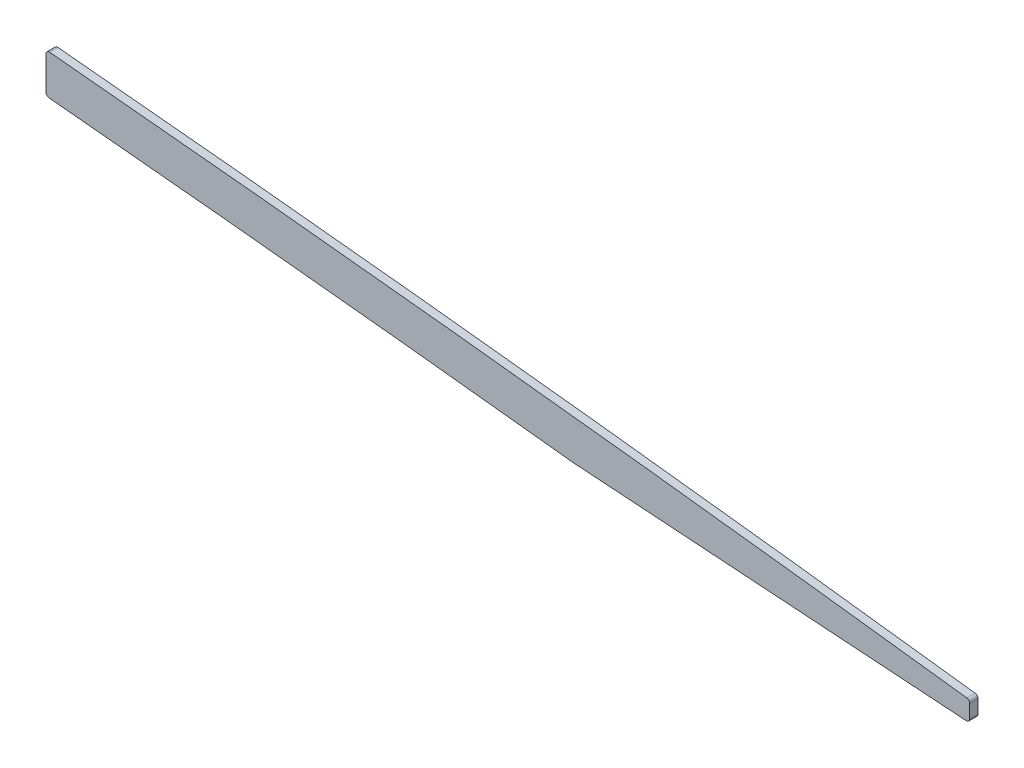
SolidWorks part; units mm, degrees
material "Plywood"
ref_plane "Front Plane" through (0, 0, 0) normal (0, 0, 1) x (1, 0, 0)
ref_plane "Top Plane" through (0, 0, 0) normal (0, 1, 0) x (1, 0, 0)
ref_plane "Right Plane" through (0, 0, 0) normal (1, 0, 0) x (0, 0, -1)
sketch "Sketch2" plane through (0, 0, 0) normal (0, 0, 1) x (1, 0, 0)
  line L0 (0, 0) -> (266.9553, 0) construction
  line L1 (825.5, 263.7287) -> (825.5, 174.6622)
  line L2 (2311.4, 135.8299) -> (2311.4, 52.664)
  line L3 (2665.4125, 96.9963) -> (2665.4125, 81.6353)
  line L4 (2665.4125, 89.3583) -> (2513.3711, 99.8062)
  spline S0 degree 5 poles (818.067, 264.7065) (827.0431, 263.4992) (836.0291, 262.3734) (845.0868, 261.3058) (891.3865, 256.087) (937.6862, 251.7792) (973.4521, 248.2277) (1071.9467, 239.0511) (1170.4413, 229.7315) (1231.7919, 224.5039) (1324.8993, 216.7906) (1418.0067, 209.0401) (1449.7429, 206.3618) (1636.9286, 190.5211) (1824.1143, 175.4092) (1979.9669, 164.2997) (2156.2686, 150.4144) (2332.5703, 133.8572) (2354.213, 131.7851) (2436.3555, 123.724) (2518.4981, 114.8591) (2579.4813, 107.7425) (2639.6368, 100.3834) (2699.7923, 92.6045) knots 77.930822 77.930822 77.930822 77.930822 77.930822 77.930822 82.465793 82.465793 82.465793 100.79329 100.79329 100.79329 131.098954 131.098954 131.098954 146.769198 146.769198 146.769198 223.533959 223.533959 223.533959 233.943117 233.943117 233.943117 264.216209 264.216209 264.216209 264.216209 264.216209 264.216209 weights 1 1 1 1 1 1 1 1 1 1 1 1 1 1 1 1 1 1 1 1 1 1 1 1
  spline S1 degree 1 poles (816.0355, 249.6025) (2697.8379, 77.4903) knots 0 0 1 1 construction
  spline S2 degree 3 poles (816.0355, 249.6025) (820.896, 248.9488) (830.6112, 247.6997) (845.2811, 245.9534) (860.0865, 244.2956) (879.8307, 242.1866) (904.37, 239.6983) (933.571, 236.8322) (962.6427, 234.0237) (991.7626, 231.242) (1021.072, 228.4759) (1060.3764, 224.797) (1109.513, 220.1844) (1168.5112, 214.8171) (1227.5001, 209.6621) (1306.1332, 203.0212) (1404.3615, 194.9207) (1522.2399, 184.9181) (1640.1829, 175.167) (1758.1654, 165.7576) (1876.1554, 156.5909) (1994.0875, 147.4533) (2092.2687, 139.6242) (2170.748, 133.0797) (2219.7717, 128.8422) (2258.984, 125.3472) (2288.3795, 122.6709) (2317.8122, 119.9317) (2347.5515, 117.1004) (2377.1599, 114.2101) (2406.4697, 111.269) (2435.8183, 108.2401) (2469.0247, 104.7153) (2497.3133, 101.6123) (2518.2453, 99.2591) (2543.5949, 96.3824) (2583.4681, 91.7389) (2626.5047, 86.5072) (2656.9573, 82.7047) (2676.2281, 80.2695) (2689.7296, 78.5389) (2697.8379, 77.4903) knots 77.930822 77.930822 77.930822 77.930822 79.386176 80.841531 82.296885 83.75224 86.662949 89.573658 92.484367 95.395077 98.305786 101.216495 107.037913 112.859332 118.68075 124.502168 136.145005 147.787842 159.430678 171.073515 182.716352 194.359189 206.002025 211.823444 217.644862 220.555571 223.46628 226.37699 229.287699 232.198408 235.109117 238.019826 240.930535 244.998119 246.453473 247.181151 252.573372 258.39479 260.13238 261.765912 264.216209 264.216209 264.216209 264.216209
  spline S3 degree 5 poles (818.067, -264.7065) (827.0431, -263.4992) (836.0291, -262.3734) (845.0868, -261.3058) (891.3865, -256.087) (937.6862, -251.7792) (973.4521, -248.2277) (1071.9467, -239.0511) (1170.4413, -229.7315) (1231.7919, -224.5039) (1324.8993, -216.7906) (1418.0067, -209.0401) (1449.7429, -206.3618) (1636.9286, -190.5211) (1824.1143, -175.4092) (1979.9669, -164.2997) (2156.2686, -150.4144) (2332.5703, -133.8572) (2354.213, -131.7851) (2436.3555, -123.724) (2518.4981, -114.8591) (2579.4813, -107.7425) (2639.6368, -100.3834) (2699.7923, -92.6045) knots 77.930822 77.930822 77.930822 77.930822 77.930822 77.930822 82.465793 82.465793 82.465793 100.79329 100.79329 100.79329 131.098954 131.098954 131.098954 146.769198 146.769198 146.769198 223.533959 223.533959 223.533959 233.943117 233.943117 233.943117 264.216209 264.216209 264.216209 264.216209 264.216209 264.216209 weights 1 1 1 1 1 1 1 1 1 1 1 1 1 1 1 1 1 1 1 1 1 1 1 1
  point P2 (0, 0)
  dimension "D1" = 818.067
  dimension "D2" = 825.5
  dimension "D3" = 2311.4
  dimension "D5" = 2665.4125
  dimension "D6" = 7.62
  dimension "D7" = 152.4
  dimension "D4" = 15.24
extrude "Boss-Extrude1" add sketch "Sketch2" along normal mid plane 3.175 contours L2 S2 L3 S0
fillet "Fillet1" radius 1.27 4 edges at (2311.4, 120.5233, 0) (2665.4125, 89.3583, 0)
